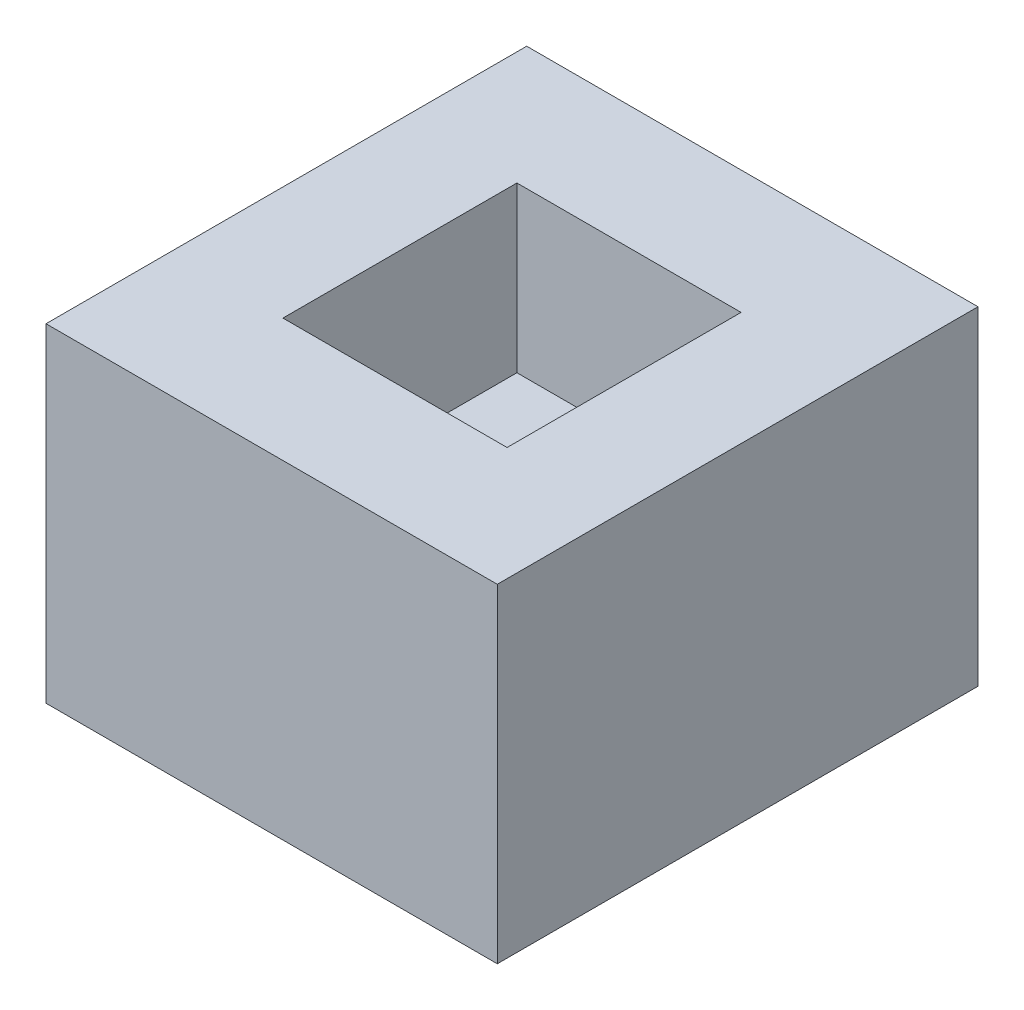
SolidWorks part; units mm, degrees
ref_plane "Front Plane" through (0, 0, 0) normal (0, 0, 1) x (1, 0, 0)
ref_plane "Top Plane" through (0, 0, 0) normal (0, 1, 0) x (1, 0, 0)
ref_plane "Right Plane" through (0, 0, 0) normal (1, 0, 0) x (0, 0, -1)
sketch "Sketch1" plane through (0, 0, 0) normal (0, 1, 0) x (1, 0, 0)
  line L1 (54.9226, -58.5022) -> (-54.9226, -58.5022)
  line L2 (54.9226, -58.5022) -> (54.9226, 58.5022)
  line L3 (54.9226, 58.5022) -> (-54.9226, 58.5022)
  line L4 (-54.9226, -58.5022) -> (-54.9226, 58.5022)
  line L5 (54.9226, -58.5022) -> (-54.9226, 58.5022) construction
  line L6 (54.9226, 58.5022) -> (-54.9226, -58.5022) construction
  point P0 (0, 0)
extrude "Boss-Extrude1" add sketch "Sketch1" along normal blind 80
sketch "Sketch2" plane through (0, 80, 0) normal (0, 1, 0) x (1, 0, 0)
  line L1 (27.2807, -28.4769) -> (-27.2807, -28.4769)
  line L2 (27.2807, -28.4769) -> (27.2807, 28.4769)
  line L3 (27.2807, 28.4769) -> (-27.2807, 28.4769)
  line L4 (-27.2807, -28.4769) -> (-27.2807, 28.4769)
  line L5 (27.2807, -28.4769) -> (-27.2807, 28.4769) construction
  line L6 (27.2807, 28.4769) -> (-27.2807, -28.4769) construction
  point P0 (0, 0)
extrude "Cut-Extrude1" cut sketch "Sketch2" against normal blind 40
